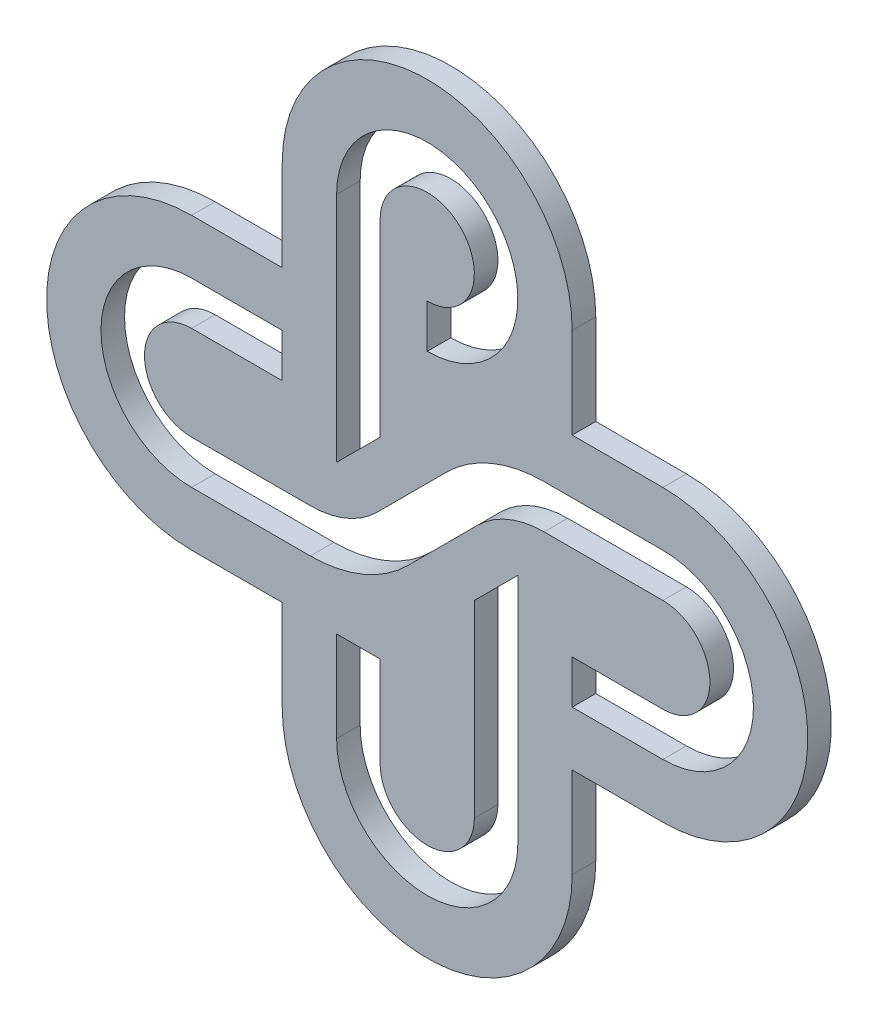
SolidWorks part; units mm, degrees
ref_plane "Front" through (0, 0, 0) normal (0, 0, 1) x (1, 0, 0)
ref_plane "Top" through (0, 0, 0) normal (0, 1, 0) x (1, 0, 0)
ref_plane "Right" through (0, 0, 0) normal (1, 0, 0) x (0, 0, -1)
sketch "Sketch2" plane through (0, 0, 0) normal (0, 0, 1) x (1, 0, 0)
  line L0 (19.5385, 19.5385) -> (31.75, 19.5385)
  line L1 (-31.75, 19.5385) -> (-19.5385, 19.5385)
  line L2 (-31.75, 19.5385) -> (-31.75, -19.5385) construction
  line L3 (-31.75, -19.5385) -> (-19.5385, -19.5385)
  line L4 (31.75, 19.5385) -> (31.75, -19.5385) construction
  line L5 (0, 31.75) -> (0, -31.75) construction
  line L6 (-31.75, 0) -> (31.75, 0) construction
  line L7 (-19.5385, 31.75) -> (19.5385, 31.75) construction
  line L8 (-19.5385, 31.75) -> (-19.5385, 19.5385)
  line L9 (-19.5385, -31.75) -> (19.5385, -31.75) construction
  line L10 (19.5385, 31.75) -> (19.5385, 19.5385)
  line L11 (-31.75, 12.2115) -> (-19.5385, 12.2115)
  line L12 (-19.5385, 12.2115) -> (-19.5385, 6.35)
  line L13 (19.5385, -19.5385) -> (31.75, -19.5385)
  line L14 (-19.5385, -19.5385) -> (-19.5385, -31.75)
  line L15 (19.5385, -19.5385) -> (19.5385, -31.75)
  line L16 (-19.5385, 6.35) -> (-31.75, 6.35)
  line L17 (-6.35, -31.75) -> (-6.35, -19.5385)
  line L18 (-6.35, -19.5385) -> (-12.2115, -19.5385)
  line L19 (-12.2115, -19.5385) -> (-12.2115, -31.75)
  line L20 (31.75, -12.2115) -> (19.5385, -12.2115)
  line L21 (19.5385, -12.2115) -> (19.5385, -6.35)
  line L22 (19.5385, -6.35) -> (31.75, -6.35)
  line L23 (0, 25.4) -> (0, 19.5385)
  line L24 (-6.35, 31.75) -> (-6.35, 6.35)
  line L25 (-6.35, 6.35) -> (-12.2115, 0.4885)
  line L26 (-12.2115, 0.4885) -> (-12.2115, 31.75)
  line L27 (6.35, -31.75) -> (6.35, -6.35)
  line L28 (6.35, -6.35) -> (12.2115, -0.4885)
  line L29 (12.2115, -0.4885) -> (12.2115, -31.75)
  line L30 (-31.75, -6.35) -> (-15.7552, -6.35)
  line L31 (-6.775, -2.6303) -> (2.6303, 6.775)
  line L32 (15.7552, 12.2115) -> (31.75, 12.2115)
  line L33 (-15.7552, -12.2115) -> (-31.75, -12.2115)
  line L34 (31.75, 6.35) -> (15.7552, 6.35)
  line L37 (-2.6303, -6.775) -> (6.775, 2.6303)
  arc A0 (-31.75, 19.5385) -> (-31.75, -19.5385) centre (-31.75, 0) ccw
  arc A1 (31.75, -19.5385) -> (31.75, 19.5385) centre (31.75, 0) ccw
  arc A2 (-19.5385, -31.75) -> (19.5385, -31.75) centre (0, -31.75) ccw
  arc A3 (19.5385, 31.75) -> (-19.5385, 31.75) centre (0, 31.75) ccw
  arc A4 (-31.75, 12.2115) -> (-31.75, -12.2115) centre (-31.75, 0) ccw
  arc A5 (-31.75, 6.35) -> (-31.75, -6.35) centre (-31.75, 0) ccw
  arc A6 (0, 19.5385) -> (-12.2115, 31.75) centre (0, 31.75) ccw
  arc A7 (0, 25.4) -> (-6.35, 31.75) centre (0, 31.75) ccw
  arc A8 (31.75, -6.35) -> (31.75, 6.35) centre (31.75, 0) ccw
  arc A9 (31.75, -12.2115) -> (31.75, 12.2115) centre (31.75, 0) ccw
  arc A10 (-6.35, -31.75) -> (6.35, -31.75) centre (0, -31.75) ccw
  arc A11 (-12.2115, -31.75) -> (12.2115, -31.75) centre (0, -31.75) ccw
  arc A12 (-15.7552, -6.35) -> (-6.775, -2.6303) centre (-15.7552, 6.35) ccw
  arc A13 (2.6303, 6.775) -> (15.7552, 12.2115) centre (15.7552, -6.35) cw
  arc A14 (15.7552, 6.35) -> (6.775, 2.6303) centre (15.7552, -6.35) ccw
  arc A16 (-15.7552, -12.2115) -> (-2.6303, -6.775) centre (-15.7552, 6.35) ccw
  dimension "D1" = 19.5385
  dimension "D3" = 12.2115
  dimension "D4" = 6.35
  dimension "D6" = 12.7
  dimension "D2" = 63.5
  dimension "D5" = 45
  dimension "D7" = 45
  dimension "D8" = 45
extrude "Boss-Extrude1" add sketch "Sketch2" along normal blind 3.175
equation "\"D1@Sketch2\"=\"D2@Sketch2\"/3.25"
equation "\"D3@Sketch2\"=\"D2@Sketch2\"/5.2"
equation "\"D4@Sketch2\"=\"D2@Sketch2\"/10"
